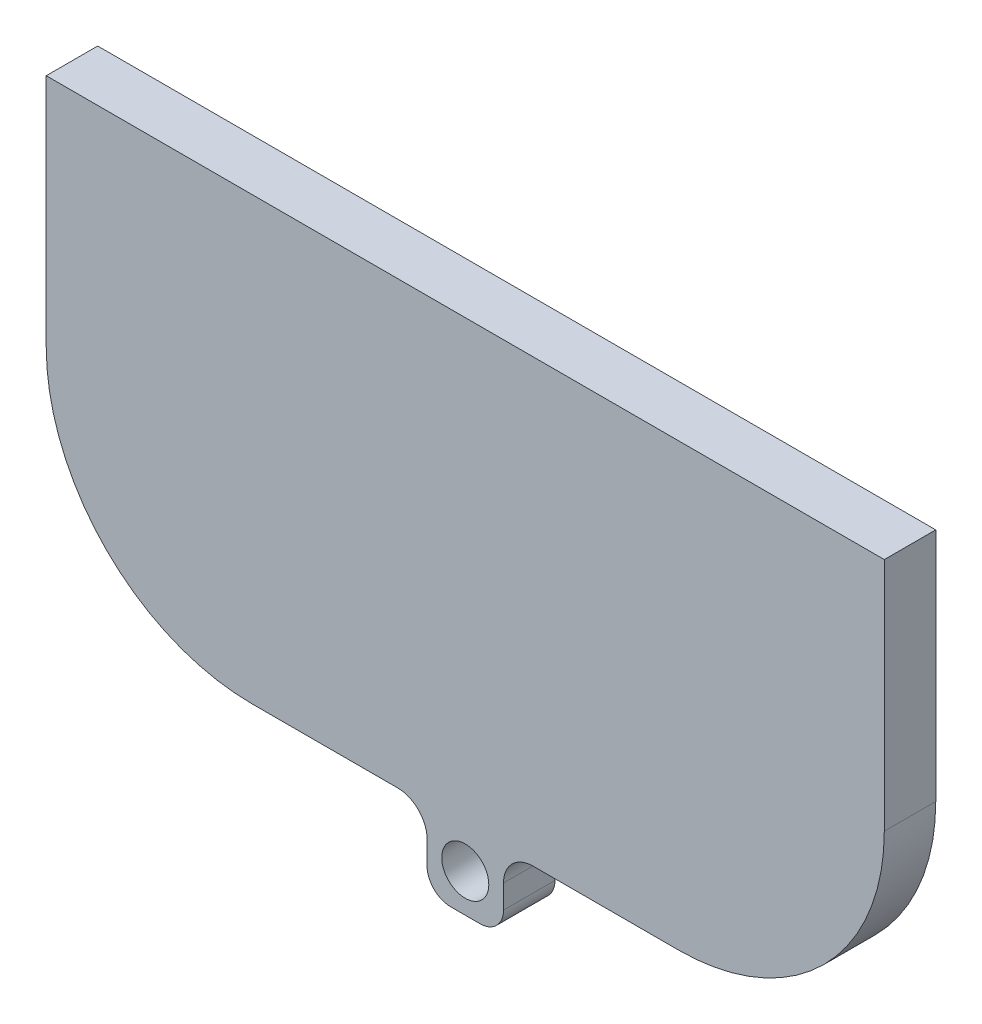
SolidWorks part; units mm, degrees
ref_plane "Front Plane" through (0, 0, 0) normal (0, 0, 1) x (1, 0, 0)
ref_plane "Top Plane" through (0, 0, 0) normal (0, 1, 0) x (1, 0, 0)
ref_plane "Right Plane" through (0, 0, 0) normal (1, 0, 0) x (0, 0, -1)
sketch "Sketch1" plane through (0, 0, 0) normal (0, 0, 1) x (1, 0, 0)
  line L0 (-24.5, 0) -> (24.5, 0)
  line L8 (28.5, 0) -> (24.5, 0)
  line L9 (24.5, 0) -> (24.5, -16)
  line L10 (14.5, -26) -> (-14.5, -26)
  line L11 (-24.5, -16) -> (-24.5, 0)
  line L12 (-24.5, 0) -> (-28.5, 0)
  line L13 (-28.5, 0) -> (-28.5, -16)
  line L14 (-14.5, -30) -> (14.5, -30)
  line L15 (28.5, -16) -> (28.5, 0)
  line L16 (28.5, 0) -> (24.5, 0)
  line L20 (-24.5, 0) -> (-28.5, 0)
  line L21 (-28.5, 0) -> (-28.5, -16)
  line L22 (-14.5, -30) -> (14.5, -30)
  line L23 (28.5, -16) -> (28.5, 0)
  arc A4 (14.5, -26) -> (24.5, -16) centre (14.5, -16) ccw
  arc A5 (-24.5, -16) -> (-14.5, -26) centre (-14.5, -16) ccw
  arc A6 (-28.5, -16) -> (-14.5, -30) centre (-14.5, -16) ccw
  arc A7 (14.5, -30) -> (28.5, -16) centre (14.5, -16) ccw
  arc A10 (-28.5, -16) -> (-14.5, -30) centre (-14.5, -16) ccw
  arc A11 (14.5, -30) -> (28.5, -16) centre (14.5, -16) ccw
  dimension "D1" = 0
extrude "Boss-Extrude1" add sketch "Sketch1" along normal blind 3.5
sketch "Sketch2" plane through (0, 0, 3.5) normal (0, 0, 1) x (1, 0, 0)
  line L0 (0, -30) -> (0, -32.6) construction
  line L1 (-14.5, -30) -> (14.5, -30) construction
  line L3 (2.6, -30) -> (-2.6, -30)
  line L4 (2.6, -30) -> (2.6, -33.6)
  line L5 (1, -35.2) -> (-1, -35.2)
  line L6 (-2.6, -30) -> (-2.6, -33.6)
  line L7 (0, -32.6) -> (2.6, -32.6) construction
  line L8 (0, -32.6) -> (0, -35.2) construction
  circle A0 centre (0, -32.6) radius 1.6
  arc A1 (-1, -35.2) -> (-2.6, -33.6) centre (-1, -33.6) cw
  arc A2 (1, -35.2) -> (2.6, -33.6) centre (1, -33.6) ccw
  point P7 (0, -30)
  point P17 (0, -30)
  dimension "D1" = 3.2
  dimension "D2" = 1.6
  dimension "D3" = 2.6
  dimension "D4" = 2.6
extrude "Boss-Extrude2" add sketch "Sketch2" against normal up to surface (3.5 mm away) contours L4 L3 L6 A1 L5 A2 | A0 up to face at (0, -16.2998, 0)
fillet "Fillet1" radius 2 2 edges at (-2.6, -30, 1.75) (2.6, -30, 1.75)
